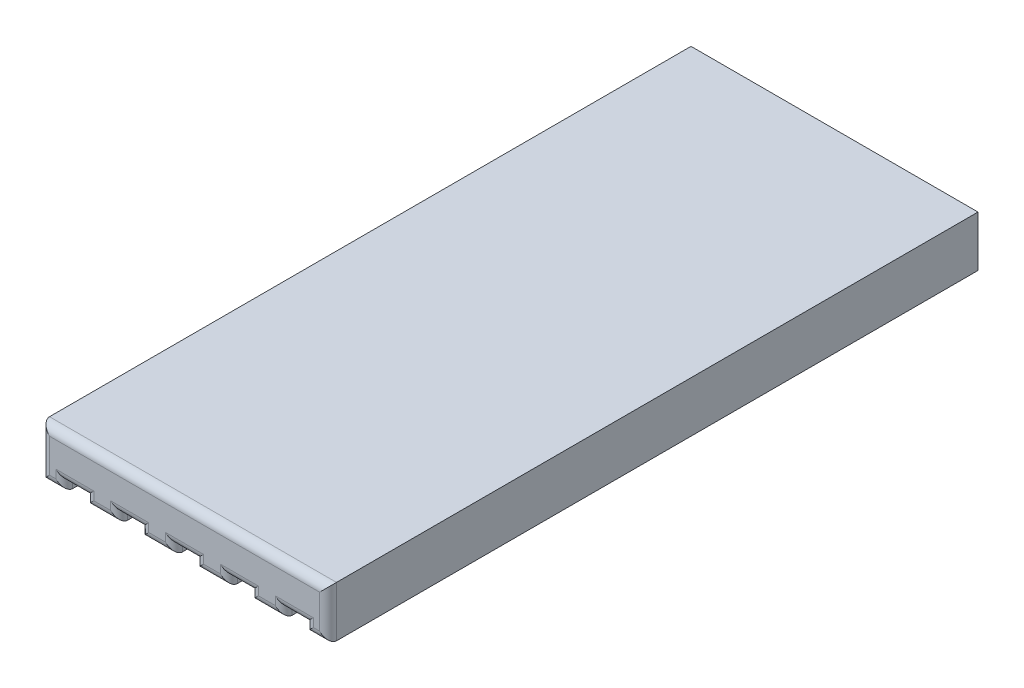
SolidWorks part; units mm, degrees
material "ABS"
ref_plane "Front Plane" through (0, 0, 0) normal (0, 0, 1) x (1, 0, 0)
ref_plane "Top Plane" through (0, 0, 0) normal (0, 1, 0) x (1, 0, 0)
ref_plane "Right Plane" through (0, 0, 0) normal (1, 0, 0) x (0, 0, -1)
sketch "Sketch1" plane through (0, 0, 0) normal (0, 1, 0) x (1, 0, 0)
  line L0 (0, -55) -> (0, 55) construction
  line L1 (-3.45, 4.8) -> (3.45, 4.8)
  line L2 (-3.45, 4.8) -> (-3.45, 3.5)
  line L3 (-3.45, 3.5) -> (3.45, 3.5)
  line L4 (3.45, 4.8) -> (3.45, 3.5)
  line L5 (-55, 0) -> (55, 0) construction
  dimension "D1" = 6.9
  dimension "D2" = 3.45
  dimension "D3" = 3.5
  dimension "D4" = 4.8
sketch "Sketch2" plane through (0, 0, -3.5) normal (0, 0, 1) x (1, 0, 0)
  line L1 (-1.7, 1.8) -> (1.7, 1.8)
  line L2 (-1.7, 1.8) -> (-1.7, 1.2)
  line L3 (-1.7, 1.2) -> (1.7, 1.2)
  line L4 (1.7, 1.8) -> (1.7, 1.2)
extrude "Boss-Extrude2" add sketch "Sketch2" along normal blind 2.7 and the other way blind 5
sketch "Sketch3" plane through (0, 0, -0.8) normal (0, 0, 1) x (1, 0, 0)
  line L1 (-1.425, 1.2) -> (-1.175, 1.2)
  line L2 (-1.425, 1.2) -> (-1.425, 1.3)
  line L3 (-1.425, 1.3) -> (-1.175, 1.3)
  line L4 (-1.175, 1.2) -> (-1.175, 1.3)
  line L5 (-1.7, 1.2) -> (1.7, 1.2) construction
  line L6 (-0.775, 1.2) -> (-0.525, 1.2)
  line L7 (-0.775, 1.2) -> (-0.775, 1.3)
  line L8 (-0.775, 1.3) -> (-0.525, 1.3)
  line L9 (-0.525, 1.2) -> (-0.525, 1.3)
  line L10 (-1.175, 1.3) -> (-0.775, 1.3) construction
  line L11 (-0.125, 1.2) -> (0.125, 1.2)
  line L12 (-0.125, 1.2) -> (-0.125, 1.3)
  line L13 (-0.125, 1.3) -> (0.125, 1.3)
  line L14 (0.125, 1.2) -> (0.125, 1.3)
  line L15 (0.525, 1.2) -> (0.775, 1.2)
  line L16 (0.525, 1.2) -> (0.525, 1.3)
  line L17 (0.525, 1.3) -> (0.775, 1.3)
  line L18 (0.775, 1.2) -> (0.775, 1.3)
  line L19 (1.175, 1.2) -> (1.425, 1.2)
  line L20 (1.175, 1.2) -> (1.175, 1.3)
  line L21 (1.175, 1.3) -> (1.425, 1.3)
  line L22 (1.425, 1.2) -> (1.425, 1.3)
  line L23 (-0.525, 1.3) -> (-0.125, 1.3) construction
  line L24 (0.125, 1.3) -> (0.525, 1.3) construction
  line L25 (0.775, 1.3) -> (1.175, 1.3) construction
  line L26 (0, -0.715) -> (0, 0.715) construction
  dimension "D1" = 0.65
  dimension "D2" = 0.25
  dimension "D3" = 0.125
  dimension "D4" = 0.1
extrude "Cut-Extrude1" cut sketch "Sketch3" against normal blind 3
fillet "Fillet1" radius 0.1 24 edges at (0, 1.8, -0.8) (1.7, 1.5, -0.8) (1.5625, 1.2, -0.8) (-1.5625, 1.2, -0.8) (-1.7, 1.5, -0.8) (0.975, 1.2, -0.8) (0.775, 1.25, -0.8) (0.65, 1.3, -0.8) (0.525, 1.25, -0.8) (0.325, 1.2, -0.8) (0.125, 1.25, -0.8) (0, 1.3, -0.8) (-0.125, 1.25, -0.8) (-0.325, 1.2, -0.8) (-0.525, 1.25, -0.8) (-0.65, 1.3, -0.8) (-0.775, 1.25, -0.8) (-0.975, 1.2, -0.8) (-1.175, 1.25, -0.8) (-1.3, 1.3, -0.8) (-1.425, 1.25, -0.8) (1.425, 1.25, -0.8) (1.3, 1.3, -0.8) (1.175, 1.25, -0.8)
equation "\"`0.5\"=1"
